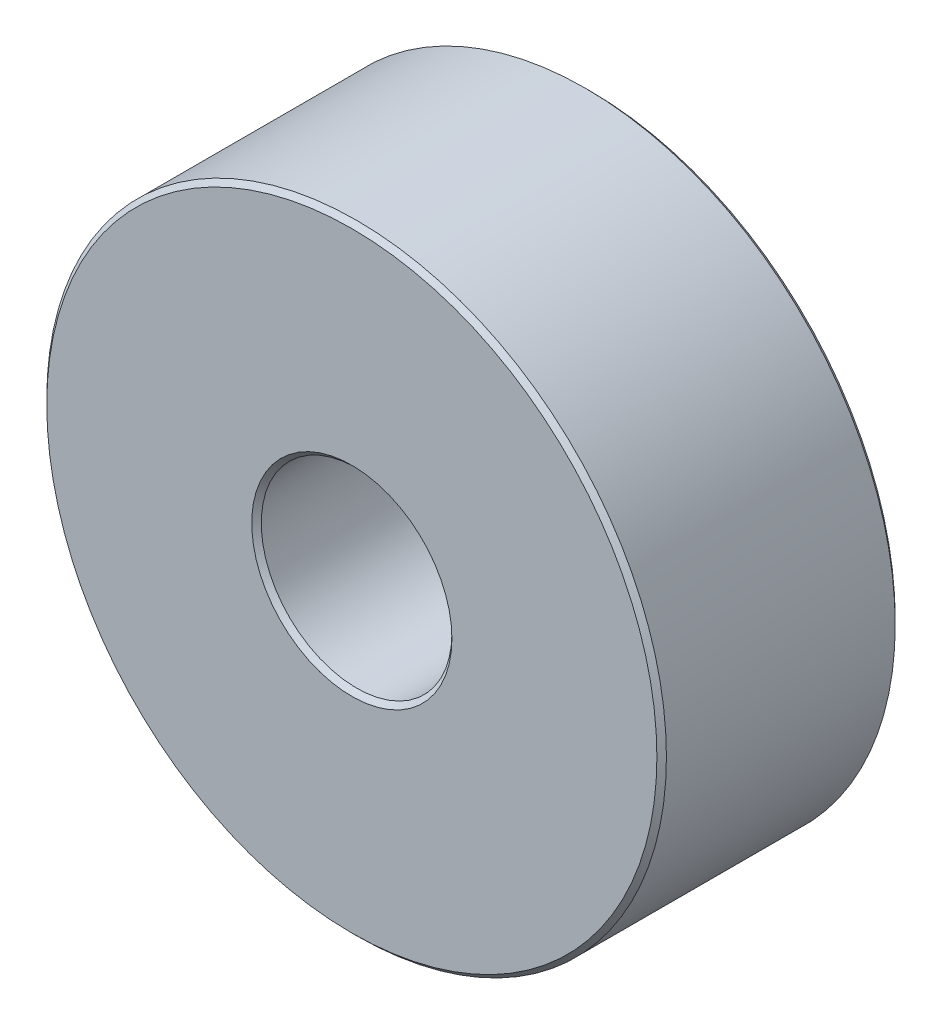
SolidWorks part; units mm, degrees
material "1060 合金"
ref_plane "前视基准面" through (0, 0, 0) normal (0, 0, 1) x (1, 0, 0)
ref_plane "上视基准面" through (0, 0, 0) normal (0, 1, 0) x (1, 0, 0)
ref_plane "右视基准面" through (0, 0, 0) normal (1, 0, 0) x (0, 0, -1)
other "Configuration Table"
sketch "草图1" plane through (0, 0, 0) normal (0, 0, 1) x (1, 0, 0)
  circle A0 centre (0, 0) radius 2
  circle A1 centre (0, 0) radius 6.5
  dimension "D1" = 4
  dimension "D2" = 13
extrude "凸台-拉伸1" add sketch "草图1" along normal mid plane 5
chamfer "倒角1" distance 0.1 angle 45 4 edges at (6.5, 0, -2.5) (2, 0, -2.5) (6.5, 0, 2.5) (2, 0, 2.5)
